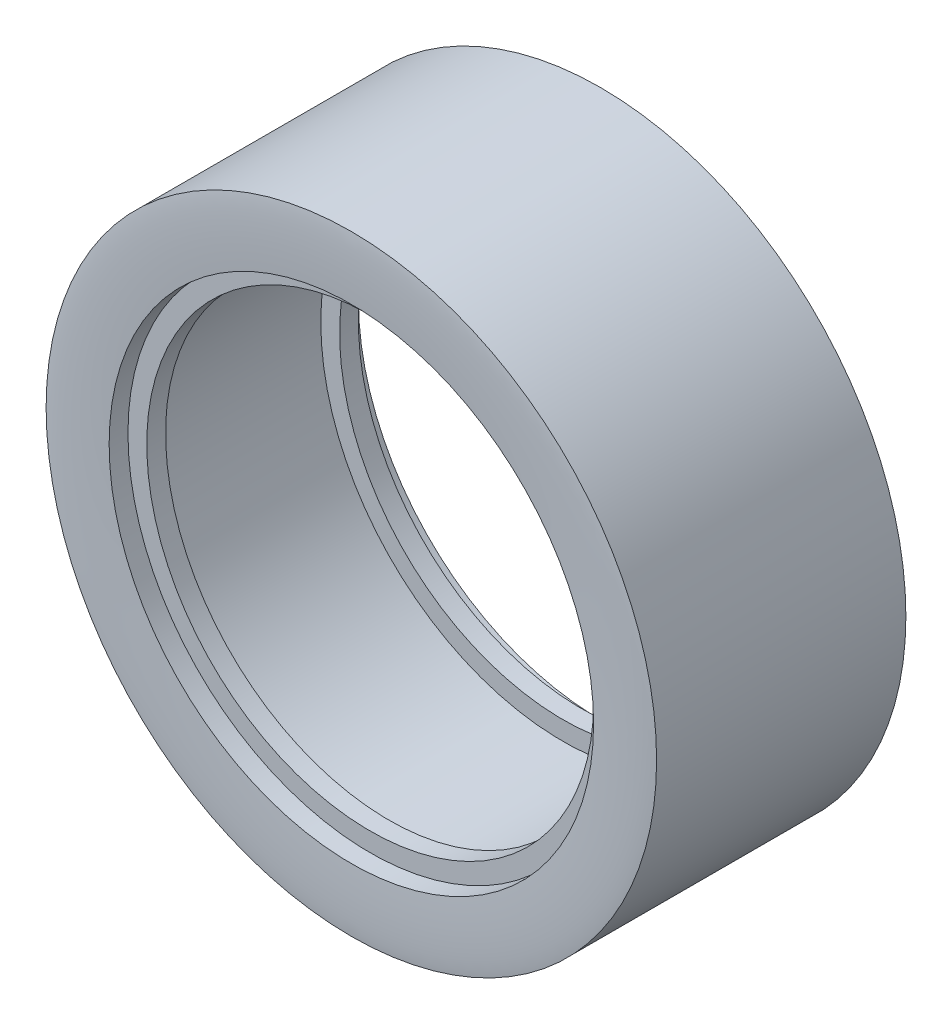
SolidWorks part; units mm, degrees
ref_plane "Front Plane" through (0, 0, 0) normal (0, 0, 1) x (1, 0, 0)
ref_plane "Top Plane" through (0, 0, 0) normal (0, 1, 0) x (1, 0, 0)
ref_plane "Right Plane" through (0, 0, 0) normal (1, 0, 0) x (0, 0, -1)
sketch "Sketch1" plane through (0, 0, 0) normal (0, 1, 0) x (1, 0, 0)
  line L0 (0, 0) -> (0, 604.3018) construction
  line L1 (32.45, 213.3501) -> (0, 213.3501) construction
  line L3 (25.75, 226.6001) -> (25.75, 224.6001)
  line L5 (32.45, 226.6001) -> (32.45, 200.1001)
  line L6 (25.75, 202.1001) -> (23.75, 202.1001)
  line L7 (25.75, 224.6001) -> (23.75, 224.6001)
  line L9 (25.75, 222.6001) -> (23.75, 222.6001)
  line L10 (23.75, 224.6001) -> (23.75, 222.6001)
  line L11 (25.75, 204.1001) -> (23.75, 204.1001)
  line L12 (23.75, 202.1001) -> (23.75, 204.1001)
  line L13 (25.75, 202.1001) -> (25.75, 200.1001)
  line L14 (25.75, 222.6001) -> (25.75, 204.1001)
  line L15 (25.75, 226.6001) -> (28.6652, 226.7729) construction
  line L16 (28.6652, 226.7729) -> (31.1065, 226.7729) construction
  line L17 (31.1065, 226.7729) -> (32.45, 226.6001) construction
  line L18 (25.75, 200.1001) -> (28.6652, 199.9274) construction
  line L19 (28.6652, 199.9274) -> (31.1065, 199.9274) construction
  line L20 (31.1065, 199.9274) -> (32.45, 200.1001) construction
  spline S0 degree 3 poles (25.75, 226.6001) (28.6652, 226.7729) (31.1065, 226.7729) (32.45, 226.6001) knots 0 0 0 0 1 1 1 1
  spline S1 degree 3 poles (25.75, 200.1001) (28.6652, 199.9274) (31.1065, 199.9274) (32.45, 200.1001) knots 0 0 0 0 1 1 1 1
  dimension "D1" = 26.5
  dimension "D2" = 6.7
  dimension "D3" = 25.75
  dimension "D4" = 2
  dimension "D5" = 2
revolve "Revolve1" add sketch "Sketch1" angle 360 about L0
